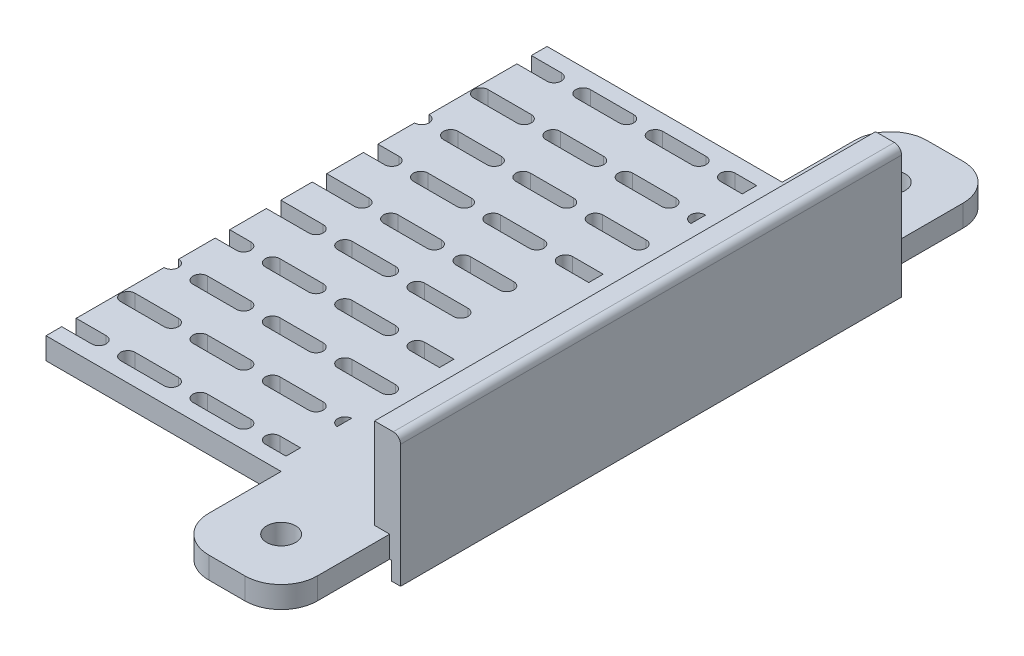
SolidWorks part; units mm, degrees
ref_plane "前视基准面" through (0, 0, 0) normal (0, 0, 1) x (1, 0, 0)
ref_plane "上视基准面" through (0, 0, 0) normal (0, 1, 0) x (1, 0, 0)
ref_plane "右视基准面" through (0, 0, 0) normal (1, 0, 0) x (0, 0, -1)
sketch "草图1" plane through (0, 0, 0) normal (0, 1, 0) x (1, 0, 0)
  line L0 (95.5, 69.25) -> (95.5, -69.25)
  line L1 (90.5, 64.25) -> (-90.5, 64.25)
  line L2 (90.5, 64.25) -> (90.5, -64.25)
  line L3 (90.5, -64.25) -> (-90.5, -64.25)
  line L4 (-90.5, 64.25) -> (-90.5, -64.25)
  line L5 (90.5, 64.25) -> (-90.5, -64.25) construction
  line L6 (90.5, -64.25) -> (-90.5, 64.25) construction
  line L7 (95.5, -69.25) -> (-95.5, -69.25)
  line L8 (-95.5, 69.25) -> (-95.5, -69.25)
  line L9 (95.5, 69.25) -> (-95.5, 69.25)
  point P0 (0, 0)
  dimension "D1" = 5
extrude "凸台-拉伸1" add sketch "草图1" along normal blind 20
sketch "草图2" plane through (0, 0, 0) normal (0, -1, 0) x (1, 0, 0)
  line L4 (-95.5, -69.25) -> (95.5, -69.25)
  line L5 (95.5, -69.25) -> (95.5, 69.25)
  line L6 (95.5, 69.25) -> (-95.5, 69.25)
  line L7 (-95.5, 69.25) -> (-95.5, -69.25)
  line L8 (-95.5, -69.25) -> (95.5, -69.25)
  line L9 (95.5, -69.25) -> (95.5, 69.25)
  line L10 (95.5, 69.25) -> (-95.5, 69.25)
  line L11 (-95.5, 69.25) -> (-95.5, -69.25)
  dimension "D1" = 0
extrude "凸台-拉伸2" add sketch "草图2" along normal blind 5
sketch "草图3" plane through (0, 0, -64.25) normal (0, 0, 1) x (1, 0, 0)
  line L4 (-90.5, 0) -> (90.5, 0)
  line L5 (90.5, 0) -> (90.5, 20)
  line L6 (90.5, 20) -> (-90.5, 20)
  line L7 (-90.5, 20) -> (-90.5, 0)
  line L8 (-90.5, 0) -> (90.5, 0)
  line L9 (90.5, 0) -> (90.5, 20)
  line L10 (90.5, 20) -> (-90.5, 20)
  line L11 (-90.5, 20) -> (-90.5, 0)
  dimension "D1" = 0
extrude "切除-拉伸1" cut sketch "草图3" against normal blind 49 and the other way blind 153
sketch "草图4" plane through (0, -5, 0) normal (0, -1, 0) x (1, 0, 0)
  line L0 (-95.5, 0) -> (-47.5, 0) construction
  line L1 (-47.5, 103) -> (47.5, 103) construction
  line L2 (-47.5, 103) -> (-47.5, -103) construction
  line L3 (-47.5, -103) -> (47.5, -103) construction
  line L4 (47.5, 103) -> (47.5, -103) construction
  line L5 (-47.5, 103) -> (47.5, -103) construction
  line L6 (-47.5, -103) -> (47.5, 103) construction
  line L7 (-95.5, 69.25) -> (-95.5, -69.25) construction
  line L8 (-95.5, 0) -> (-95.5, -35)
  line L9 (-95.5, -35) -> (-90.5, -35)
  line L10 (-90.5, -35) -> (-90.5, 35)
  line L11 (-90.5, 35) -> (-95.5, 35)
  line L12 (-95.5, 35) -> (-95.5, 0)
  line L13 (0, 0) -> (0, 35) construction
  line L14 (95.5, 35) -> (95.5, 0)
  line L15 (90.5, 35) -> (95.5, 35)
  line L16 (90.5, -35) -> (90.5, 35)
  line L17 (95.5, -35) -> (90.5, -35)
  line L18 (95.5, 0) -> (95.5, -35)
  point P0 (0, 0)
extrude "凸台-拉伸3" add sketch "草图4" along normal blind 49
sketch "草图5" plane through (0, -54, 0) normal (0, -1, 0) x (1, 0, 0)
  line L4 (-95.5, 35) -> (-95.5, -35)
  line L5 (-95.5, -35) -> (-90.5, -35)
  line L6 (-90.5, -35) -> (-90.5, 35)
  line L7 (-90.5, 35) -> (-95.5, 35)
  line L8 (-95.5, 35) -> (-95.5, -35)
  line L9 (-95.5, -35) -> (-90.5, -35)
  line L10 (-90.5, -35) -> (-90.5, 35)
  line L11 (-90.5, 35) -> (-95.5, 35)
  line L12 (95.5, 35) -> (90.5, 35)
  line L13 (90.5, 35) -> (90.5, -35)
  line L14 (90.5, -35) -> (95.5, -35)
  line L15 (95.5, -35) -> (95.5, 35)
  line L16 (95.5, 35) -> (90.5, 35)
  line L17 (90.5, 35) -> (90.5, -35)
  line L18 (90.5, -35) -> (95.5, -35)
  line L19 (95.5, -35) -> (95.5, 35)
  dimension "D1" = 0
  dimension "D2" = 0
extrude "凸台-拉伸4" add sketch "草图5" along normal blind 34
sketch "草图7" plane through (-95.5, 0, 0) normal (-1, 0, 0) x (0, 0, 1)
  line L0 (35, -88) -> (-35, -88)
  line L1 (-35, -88) -> (-35, -83)
  line L2 (-35, -88) -> (-35, -5) construction
  line L3 (-35, -83) -> (35, -83)
  line L4 (35, -88) -> (35, -5) construction
  line L5 (35, -83) -> (35, -88)
extrude "凸台-拉伸5" add sketch "草图7" along normal blind 37
sketch "草图8" plane through (95.5, 0, 0) normal (1, 0, 0) x (0, 0, -1)
  line L4 (-35, -83) -> (-35, -88)
  line L5 (35, -83) -> (-35, -83)
  line L6 (35, -88) -> (35, -83)
  line L7 (-35, -88) -> (35, -88)
  line L8 (-35, -83) -> (-35, -88)
  line L9 (35, -83) -> (-35, -83)
  line L10 (35, -88) -> (35, -83)
  line L11 (-35, -88) -> (35, -88)
  dimension "D1" = 0
extrude "凸台-拉伸6" add sketch "草图8" along normal blind 37
sketch "草图12" plane through (0, -5, 0) normal (0, -1, 0) x (1, 0, 0)
  line L0 (0, 0) -> (0, -50.9491) construction
  line L1 (0, 0) -> (21.7152, 0) construction
  line L6 (90.5, 35) -> (95.5, 35)
  line L7 (90.5, 35) -> (95.5, 35)
  line L8 (95.5, -69.25) -> (95.5, -35)
  line L9 (95.5, -35) -> (90.5, -35)
  line L10 (90.5, -35) -> (90.5, 35)
  line L11 (95.5, 35) -> (95.5, 69.25)
  line L15 (95.5, -35) -> (90.5, -35) construction
  line L16 (90.5, -35) -> (90.5, 35) construction
  line L20 (95.5, -69.25) -> (95.5, -35)
  line L27 (95.5, 35) -> (95.5, 69.25)
  line L28 (95.5, 69.25) -> (-95.5, 69.25)
  line L29 (95.5, 69.25) -> (-95.5, 69.25)
  line L30 (-95.5, 69.25) -> (-95.5, 35)
  line L31 (-95.5, 69.25) -> (-95.5, 35)
  line L32 (-95.5, 35) -> (-90.5, 35)
  line L33 (-95.5, 35) -> (-90.5, 35)
  line L34 (-90.5, 35) -> (-90.5, -35)
  line L35 (-90.5, 35) -> (-90.5, -35)
  line L36 (-90.5, -35) -> (-95.5, -35)
  line L37 (-90.5, -35) -> (-95.5, -35)
  line L38 (-95.5, -35) -> (-95.5, -69.25)
  line L39 (-95.5, -35) -> (-95.5, -69.25)
  line L40 (-95.5, -69.25) -> (95.5, -69.25)
  line L41 (-95.5, -69.25) -> (95.5, -69.25)
  circle A0 centre (48, -35) radius 12.5
  circle A1 centre (-48, -35) radius 12.5
  circle A2 centre (48, 35) radius 12.5
  circle A3 centre (-48, 35) radius 12.5
  dimension "D1" = 0
sketch "草图16" plane through (0, -88, 0) normal (0, -1, 0) x (1, 0, 0)
  line L0 (132.5, 35) -> (117.5, 35)
  line L1 (132.5, 35) -> (90.5, 35) construction
  line L2 (117.5, 35) -> (117.5, -35)
  line L3 (90.5, -35) -> (132.5, -35) construction
  line L4 (117.5, -35) -> (132.5, -35)
  line L5 (132.5, -35) -> (132.5, 35)
  line L6 (-132.5, -35) -> (-117.5, -35)
  line L7 (-132.5, -35) -> (-90.5, -35) construction
  line L8 (-117.5, -35) -> (-117.5, 35)
  line L9 (-90.5, 35) -> (-132.5, 35) construction
  line L10 (-117.5, 35) -> (-132.5, 35)
  line L11 (-132.5, 35) -> (-132.5, -35)
extrude "切除-拉伸7" cut sketch "草图16" against normal blind 62
extrude "切除-拉伸9" cut sketch "草图12" against normal blind 20 contours A0 | A1 | A3 | A2
sketch "草图19" plane through (117.5, 0, 0) normal (1, 0, 0) x (0, 0, -1)
  line L4 (-35, -83) -> (-35, -88)
  line L5 (-35, -88) -> (35, -88)
  line L6 (35, -88) -> (35, -83)
  line L7 (35, -83) -> (-35, -83)
  line L8 (-35, -83) -> (-35, -88)
  line L9 (-35, -88) -> (35, -88)
  line L10 (35, -88) -> (35, -83)
  line L11 (35, -83) -> (-35, -83)
  dimension "D1" = 0
extrude "切除-拉伸10" cut sketch "草图19" against normal blind 3.5
sketch "草图20" plane through (-117.5, 0, 0) normal (-1, 0, 0) x (0, 0, 1)
  line L4 (-35, -83) -> (-35, -88)
  line L5 (-35, -88) -> (35, -88)
  line L6 (35, -88) -> (35, -83)
  line L7 (35, -83) -> (-35, -83)
  line L8 (-35, -83) -> (-35, -88)
  line L9 (-35, -88) -> (35, -88)
  line L10 (35, -88) -> (35, -83)
  line L11 (35, -83) -> (-35, -83)
  dimension "D1" = 0
extrude "切除-拉伸11" cut sketch "草图20" against normal blind 3.5
sketch "草图21" plane through (0, -83, 0) normal (0, 1, 0) x (1, 0, 0)
  line L0 (-114, 0) -> (-95.5, 0) construction
  line L1 (-114, -35) -> (-114, 35) construction
  line L2 (-95.5, -35) -> (-95.5, 35) construction
  line L3 (-104.75, 0) -> (-104.75, -35) construction
  line L4 (-114, -35) -> (-95.5, -35) construction
  line L5 (0, 0) -> (0, 27.7926) construction
  circle A0 centre (-104.75, -17.5) radius 4
  circle A1 centre (-104.75, 17.5) radius 4
  circle A2 centre (104.75, -17.5) radius 4
  circle A3 centre (104.75, 17.5) radius 4
extrude "切除-拉伸12" cut sketch "草图21" against normal through all
fillet "圆角5" radius 10 4 edges at (114, -85.5, -35) (114, -85.5, 35) (-114, -85.5, 35) (-114, -85.5, -35)
sketch "草图22" plane through (90.5, 0, 0) normal (-1, 0, 0) x (0, 0, 1)
  line L6 (35, -88) -> (35, -5)
  line L7 (35, -5) -> (-35, -5)
  line L10 (-35, -5) -> (-35, -88)
  line L11 (-35, -88) -> (35, -88)
  line L12 (35, -88) -> (35, -5)
  line L13 (35, -5) -> (-35, -5)
  line L16 (-35, -5) -> (-35, -88)
  line L17 (-35, -88) -> (35, -88)
  dimension "D1" = 0
extrude "切除-拉伸13" cut sketch "草图22" against normal blind 54
sketch "草图23" plane through (-90.5, 0, 0) normal (1, 0, 0) x (0, 0, -1)
  line L6 (35, -5) -> (-35, -5)
  line L7 (-35, -5) -> (-35, -88)
  line L8 (-35, -88) -> (35, -88)
  line L9 (35, -88) -> (35, -5)
  line L12 (35, -5) -> (-35, -5)
  line L13 (-35, -5) -> (-35, -88)
  line L14 (-35, -88) -> (35, -88)
  line L15 (35, -88) -> (35, -5)
  dimension "D1" = 0
extrude "切除-拉伸14" cut sketch "草图23" against normal blind 54
sketch "草图24" plane through (0, -5, 0) normal (0, -1, 0) x (1, 0, 0)
  circle A1 centre (80.5, 18.25) radius 2
  circle A3 centre (80.5, -19.75) radius 2
extrude "切除-拉伸15" cut sketch "草图24" against normal blind 10
sketch "草图25" plane through (0, 0, 0) normal (0, 1, 0) x (1, 0, 0)
  circle A0 centre (80.5, -18.25) radius 4
  circle A1 centre (80.5, 19.75) radius 4
sketch "草图26" plane through (0, 0, 0) normal (0, 1, 0) x (1, 0, 0)
  line L4 (90.5, -69.25) -> (90.5, 69.25)
  line L5 (90.5, 69.25) -> (-90.5, 69.25)
  line L6 (-90.5, 69.25) -> (-90.5, -69.25)
  line L7 (-90.5, -69.25) -> (90.5, -69.25)
  line L8 (90.5, -69.25) -> (90.5, 69.25)
  line L9 (90.5, 69.25) -> (-90.5, 69.25)
  line L10 (-90.5, 69.25) -> (-90.5, -69.25)
  line L11 (-90.5, -69.25) -> (90.5, -69.25)
  circle A0 centre (48, -35) radius 12.5 construction
  circle A1 centre (48, -35) radius 12.5
  circle A2 centre (48, 35) radius 12.5 construction
  circle A3 centre (48, 35) radius 12.5
  circle A4 centre (-48, -35) radius 12.5 construction
  circle A5 centre (-48, -35) radius 12.5
  circle A6 centre (-48, 35) radius 12.5 construction
  circle A7 centre (-48, 35) radius 12.5
  dimension "D1" = 0
extrude "凸台-拉伸8" add sketch "草图26" along normal blind 1
extrude "切除-拉伸16" cut sketch "草图25" along normal blind 1 and the other way blind 4
mirror "镜向1" about plane through (0, 0, 0) normal (1, 0, 0) of "切除-拉伸15", "切除-拉伸16"
sketch "草图28" plane through (0, 1, 0) normal (0, 1, 0) x (1, 0, 0)
  circle A0 centre (-80.5, -18.25) radius 4 construction
  circle A1 centre (-80.5, -18.25) radius 4
  circle A2 centre (-80.5, 19.75) radius 4 construction
  circle A3 centre (-80.5, 19.75) radius 4
  circle A4 centre (80.5, -18.25) radius 4 construction
  circle A5 centre (80.5, -18.25) radius 4
  circle A6 centre (80.5, 19.75) radius 4 construction
  circle A7 centre (80.5, 19.75) radius 4
extrude "凸台-拉伸9" add sketch "草图28" against normal up to surface (6 mm away) up to face at (-80.5, -5, 16.25)
sketch "草图29" plane through (0, -5, 0) normal (0, -1, 0) x (1, 0, 0)
  line L0 (95.5, 69.25) -> (95, 69.25)
  line L1 (-95, 0) -> (-95, 69.25)
  line L2 (95.5, 69.25) -> (-95.5, 69.25) construction
  line L3 (-95, 69.25) -> (-95.5, 69.25)
  line L4 (-95.5, 69.25) -> (-95.5, -69.25)
  line L5 (-95.5, -69.25) -> (-95, -69.25)
  line L6 (-95.5, -69.25) -> (95.5, -69.25) construction
  line L7 (-95, -69.25) -> (-95, 0)
  line L8 (95, 69.25) -> (95, -69.25)
  line L9 (95, -69.25) -> (95.5, -69.25)
  line L10 (95.5, -69.25) -> (95.5, 69.25)
extrude "切除-拉伸18" cut sketch "草图29" against normal blind 50
sketch "草图31" plane through (0, -5, 0) normal (0, -1, 0) x (1, 0, 0)
  line L0 (-95, 69.25) -> (-95, 89.25)
  line L1 (-85, 99.25) -> (-75, 99.25)
  line L2 (-65, 89.25) -> (-65, 69.25)
  line L3 (95, 69.25) -> (-95, 69.25) construction
  line L4 (-65, 69.25) -> (-95, 69.25)
  line L5 (-80, 99.25) -> (-80, 69.25) construction
  line L6 (-80, 84.25) -> (-65, 84.25) construction
  line L7 (0, 0) -> (19.0311, 0) construction
  line L8 (0, 0) -> (0, -16.3488) construction
  line L9 (-65, -89.25) -> (-65, -69.25)
  line L10 (-85, -99.25) -> (-75, -99.25)
  line L11 (-95, -69.25) -> (-95, -89.25)
  line L12 (-65, -69.25) -> (-95, -69.25)
  line L13 (80, 84.25) -> (65, 84.25) construction
  line L14 (80, 99.25) -> (80, 69.25) construction
  line L15 (65, -69.25) -> (95, -69.25)
  line L16 (95, -69.25) -> (95, -89.25)
  line L17 (85, -99.25) -> (75, -99.25)
  line L18 (65, -89.25) -> (65, -69.25)
  line L19 (65, 69.25) -> (95, 69.25)
  line L20 (65, 89.25) -> (65, 69.25)
  line L21 (85, 99.25) -> (75, 99.25)
  line L22 (95, 69.25) -> (95, 89.25)
  arc A0 (-65, 89.25) -> (-75, 99.25) centre (-75, 89.25) ccw
  arc A1 (-95, 89.25) -> (-85, 99.25) centre (-85, 89.25) cw
  circle A2 centre (-80, 84.25) radius 4
  circle A3 centre (-80, -84.25) radius 4
  arc A4 (-65, -89.25) -> (-75, -99.25) centre (-75, -89.25) cw
  arc A5 (-95, -89.25) -> (-85, -99.25) centre (-85, -89.25) ccw
  arc A6 (95, -89.25) -> (85, -99.25) centre (85, -89.25) cw
  arc A7 (65, -89.25) -> (75, -99.25) centre (75, -89.25) ccw
  circle A8 centre (80, -84.25) radius 4
  circle A9 centre (80, 84.25) radius 4
  arc A10 (95, 89.25) -> (85, 99.25) centre (85, 89.25) ccw
  arc A11 (65, 89.25) -> (75, 99.25) centre (75, 89.25) cw
  dimension "D1" = 10
extrude "凸台-拉伸10" add sketch "草图31" against normal up to surface (6 mm away) up to face at (-48, 1, 47.5)
sketch "草图32" plane through (0, 20, 0) normal (0, 1, 0) x (1, 0, 0)
  line L0 (90.5, 69.25) -> (91.3, 69.25)
  line L4 (95, 69.25) -> (90.5, 69.25) construction
  line L5 (90.5, -69.25) -> (90.5, 69.25) construction
  line L6 (90.5, -69.25) -> (90.5, 69.25)
  line L7 (91.3, 69.25) -> (91.3, -69.25)
  line L8 (90.5, -69.25) -> (95, -69.25) construction
  line L9 (91.3, -69.25) -> (90.5, -69.25)
  line L10 (-90.5, -69.25) -> (-91.3, -69.25)
  line L11 (-95, -69.25) -> (-90.5, -69.25) construction
  line L12 (-91.3, -69.25) -> (-91.3, 69.25)
  line L13 (-90.5, 69.25) -> (-95, 69.25) construction
  line L14 (-91.3, 69.25) -> (-90.5, 69.25)
  line L15 (-90.5, 69.25) -> (-90.5, -69.25) construction
  line L16 (-90.5, 69.25) -> (-90.5, -69.25)
extrude "切除-拉伸19" cut sketch "草图32" against normal up to surface (19 mm away) up to face at (-48, 1, 47.5)
sketch "草图33" plane through (0, 20, 0) normal (0, 1, 0) x (1, 0, 0)
  line L4 (91.3, 69.25) -> (91.3, -69.25)
  line L5 (91.3, -69.25) -> (95, -69.25)
  line L6 (95, -69.25) -> (95, 69.25)
  line L7 (95, 69.25) -> (91.3, 69.25)
  line L8 (91.3, 69.25) -> (91.3, -69.25)
  line L9 (91.3, -69.25) -> (95, -69.25)
  line L10 (95, -69.25) -> (95, 69.25)
  line L11 (95, 69.25) -> (91.3, 69.25)
  line L12 (-91.3, -69.25) -> (-91.3, 69.25)
  line L13 (-91.3, 69.25) -> (-95, 69.25)
  line L14 (-95, 69.25) -> (-95, -69.25)
  line L15 (-95, -69.25) -> (-91.3, -69.25)
  line L16 (-91.3, -69.25) -> (-91.3, 69.25)
  line L17 (-91.3, 69.25) -> (-95, 69.25)
  line L18 (-95, 69.25) -> (-95, -69.25)
  line L19 (-95, -69.25) -> (-91.3, -69.25)
  dimension "D1" = 0
  dimension "D2" = 0
extrude "凸台-拉伸11" add sketch "草图33" along normal blind 6
sketch "草图34" plane through (0, -5, 0) normal (0, -1, 0) x (1, 0, 0)
  circle A0 centre (-48, -35) radius 12.5 construction
  circle A1 centre (-48, -35) radius 12.5
  circle A2 centre (-48, 35) radius 12.5 construction
  circle A3 centre (-48, 35) radius 12.5
  circle A4 centre (48, -35) radius 12.5 construction
  circle A5 centre (48, -35) radius 12.5
  circle A6 centre (48, 35) radius 12.5 construction
  circle A7 centre (48, 35) radius 12.5
extrude "凸台-拉伸12" add sketch "草图34" against normal up to surface (6 mm away) up to face at (0, 1, 0)
sketch "草图35" plane through (0, -5, 0) normal (0, -1, 0) x (1, 0, 0)
  line L0 (65, -69.25) -> (62, -69.25)
  line L2 (65, 69.25) -> (65, -69.25)
  line L6 (-65, -69.25) -> (65, -69.25) construction
  line L8 (62, -69.25) -> (62, 69.25)
  line L9 (65, 69.25) -> (-65, 69.25) construction
  line L10 (62, 69.25) -> (65, 69.25)
  line L11 (-65, -69.25) -> (-62, -69.25)
  line L12 (-62, -69.25) -> (-62, 69.25)
  line L13 (-62, 69.25) -> (-65, 69.25)
  line L14 (-65, 69.25) -> (-65, 89.25) construction
  line L15 (-65, 69.25) -> (-65, -69.25)
  point P0 (0, 0)
extrude "凸台-拉伸13" add sketch "草图35" along normal blind 5
sketch "草图36" plane through (-95, 0, 0) normal (-1, 0, 0) x (0, 0, 1)
  line L0 (-69.25, -10) -> (-69.25, -5) construction
  line L1 (-69.25, -10) -> (-69.25, -5)
  line L2 (69.25, -10) -> (69.25, -5) construction
  line L3 (69.25, -10) -> (69.25, -5)
  line L7 (-69.25, 26) -> (69.25, 26) construction
  line L8 (-69.25, 26) -> (69.25, 26)
  line L9 (69.25, 26) -> (69.25, 1) construction
  line L10 (69.25, 26) -> (69.25, 1)
  line L13 (-69.25, -10) -> (69.25, -10)
  line L16 (-69.25, 26) -> (-69.25, 1) construction
  line L17 (-69.25, 26) -> (-69.25, 1)
  line L18 (-69.25, 1) -> (-69.25, -5)
  line L19 (69.25, -5) -> (69.25, 1)
extrude "凸台-拉伸14" add sketch "草图36" along normal blind 3
sketch "草图37" plane through (-95, 0, 0) normal (1, 0, 0) x (0, 0, -1)
  line L4 (69.25, -5) -> (-69.25, -5)
  line L5 (-69.25, -5) -> (-69.25, -10)
  line L6 (-69.25, -10) -> (69.25, -10)
  line L7 (69.25, -10) -> (69.25, -5)
  line L8 (69.25, -5) -> (-69.25, -5)
  line L9 (-69.25, -5) -> (-69.25, -10)
  line L10 (-69.25, -10) -> (69.25, -10)
  line L11 (69.25, -10) -> (69.25, -5)
  dimension "D1" = 0
extrude "切除-拉伸20" cut sketch "草图37" against normal blind 0.5
mirror "镜向2" about plane through (0, 0, 0) normal (1, 0, 0) of "切除-拉伸20", "凸台-拉伸14"
sketch "草图38" plane through (0, -5, 0) normal (0, -1, 0) x (1, 0, 0)
  line L2 (0, 0) -> (62, 0)
  line L3 (62, 69.25) -> (62, -69.25) construction
  line L4 (0, -2.5) -> (-62, -2.5)
  line L5 (0, -2.5) -> (62, -2.5)
  line L6 (0, 2.5) -> (-62, 2.5)
  line L7 (0, 2.5) -> (62, 2.5)
  line L8 (-62, -69.25) -> (-62, 69.25) construction
  line L9 (-62, -2.5) -> (-62, 2.5)
  line L10 (62, 69.25) -> (62, -69.25) construction
  line L11 (62, 2.5) -> (62, -2.5)
  line L12 (0, 0) -> (-62, 0) construction
  dimension "D1" = 2.5
  dimension "D2" = 2.5
extrude "凸台-拉伸15" add sketch "草图38" along normal up to surface (5 mm away) contours L6 L9 L4 L5 L11 L7 up to face at (-63.5, -10, 0)
sketch "草图40" plane through (0, -5, 0) normal (0, -1, 0) x (1, 0, 0)
  line L0 (0, 0) -> (0, 69.25) construction
  line L1 (62, 69.25) -> (-62, 69.25) construction
  line L2 (0, 34.625) -> (-12, 34.625) construction
  line L3 (0, 34.625) -> (-32.125, 2.5) construction
  line L4 (0, 32.625) -> (-12, 32.625)
  line L5 (0, 36.625) -> (-12, 36.625)
  line L6 (62, 2.5) -> (-62, 2.5) construction
  line L7 (25, 34.625) -> (13, 34.625) construction
  line L8 (25, 32.625) -> (13, 32.625)
  line L9 (25, 36.625) -> (13, 36.625)
  line L10 (50, 34.625) -> (38, 34.625) construction
  line L11 (50, 32.625) -> (38, 32.625)
  line L12 (50, 36.625) -> (38, 36.625)
  line L13 (-25, 34.625) -> (-37, 34.625) construction
  line L14 (-25, 32.625) -> (-37, 32.625)
  line L15 (-25, 36.625) -> (-37, 36.625)
  arc A0 (0, 32.625) -> (0, 36.625) centre (0, 34.625) ccw
  arc A1 (-12, 36.625) -> (-12, 32.625) centre (-12, 34.625) ccw
  arc A2 (25, 32.625) -> (25, 36.625) centre (25, 34.625) ccw
  arc A3 (13, 36.625) -> (13, 32.625) centre (13, 34.625) ccw
  arc A4 (50, 32.625) -> (50, 36.625) centre (50, 34.625) ccw
  arc A5 (38, 36.625) -> (38, 32.625) centre (38, 34.625) ccw
  arc A6 (-25, 32.625) -> (-25, 36.625) centre (-25, 34.625) ccw
  arc A7 (-37, 36.625) -> (-37, 32.625) centre (-37, 34.625) ccw
  point P9 (-6, 34.625)
  point P20 (19, 34.625)
  point P27 (44, 34.625)
  point P34 (-31, 34.625)
  dimension "D1" = 45
  dimension "D2" = 3
  dimension "D3" = 2
extrude "切除-拉伸22" cut sketch "草图40" against normal through all contours L5 A1 L4 A0
sketch "草图41" plane through (0, -5, 0) normal (0, -1, 0) x (1, 0, 0)
  line L0 (0, 0) -> (0, 69.25)
  line L1 (62, 69.25) -> (-62, 69.25) construction
  line L2 (0, 34.625) -> (-32.125, 2.5)
  line L3 (62, 2.5) -> (-62, 2.5) construction
  dimension "D1" = 45
pattern_linear "阵列(线性)1" count 3 spacing 20 along (-0.7071, 0, -0.7071) of "切除-拉伸22"
pattern_linear "阵列(线性)2" count 3 spacing 20 along (0.7071, 0, 0.7071) of "切除-拉伸22"
pattern_linear "阵列(线性)3" count 5 spacing 20 along (1, 0, 0) of "阵列(线性)2", "阵列(线性)1", "切除-拉伸22"
sketch "草图42" plane through (0, 1, 0) normal (0, 1, 0) x (1, 0, 0)
  line L0 (82.1421, -50.7671) -> (91.3, -50.7671) construction
  line L1 (82.1421, -50.7671) -> (91.3, -50.7671)
  line L2 (82.1421, -46.7671) -> (91.3, -46.7671) construction
  line L3 (82.1421, -46.7671) -> (91.3, -46.7671)
  line L4 (94.1421, -46.7671) -> (91.3, -46.7671) construction
  line L5 (94.1421, -46.7671) -> (91.3, -46.7671)
  line L6 (94.1421, -50.7671) -> (91.3, -50.7671) construction
  line L7 (94.1421, -50.7671) -> (91.3, -50.7671)
  line L8 (98, -64.9093) -> (96.2843, -64.9093) construction
  line L9 (98, -64.9093) -> (96.2843, -64.9093)
  line L10 (98, -60.9093) -> (96.2843, -60.9093) construction
  line L11 (98, -60.9093) -> (96.2843, -60.9093)
  line L12 (98, -64.9093) -> (98, -60.9093) construction
  line L13 (98, -64.9093) -> (98, -60.9093)
  line L14 (76.2843, -60.9093) -> (88.2843, -60.9093) construction
  line L15 (76.2843, -60.9093) -> (88.2843, -60.9093)
  line L16 (76.2843, -64.9093) -> (88.2843, -64.9093) construction
  line L17 (76.2843, -64.9093) -> (88.2843, -64.9093)
  line L20 (56.2843, -60.9093) -> (68.2843, -60.9093) construction
  line L21 (65, -60.9093) -> (68.2843, -60.9093)
  line L22 (56.2843, -64.9093) -> (68.2843, -64.9093) construction
  line L23 (65, -64.9093) -> (68.2843, -64.9093)
  line L26 (62.1421, -50.7671) -> (74.1421, -50.7671) construction
  line L27 (62.1421, -46.7671) -> (74.1421, -46.7671) construction
  line L28 (65, -50.7671) -> (74.1421, -50.7671)
  line L29 (65, -46.7671) -> (74.1421, -46.7671)
  line L30 (68, -32.625) -> (80, -32.625) construction
  line L31 (68, -36.625) -> (80, -36.625) construction
  line L32 (68, -32.625) -> (80, -32.625)
  line L33 (68, -36.625) -> (80, -36.625)
  line L34 (53.8579, -22.4829) -> (65.8579, -22.4829) construction
  line L35 (53.8579, -18.4829) -> (65.8579, -18.4829) construction
  line L37 (65, -22.4829) -> (65.8579, -22.4829)
  line L38 (65, -18.4829) -> (65.8579, -18.4829)
  line L44 (62, -64.9093) -> (65, -64.9093)
  line L45 (65, -64.9093) -> (65, -60.9093)
  line L46 (65, -60.9093) -> (62, -60.9093)
  line L47 (62, -60.9093) -> (62, -64.9093)
  line L48 (62, -64.9093) -> (65, -64.9093)
  line L49 (62.1421, -50.7671) -> (65, -50.7671)
  line L50 (65, -60.9093) -> (62, -60.9093)
  line L51 (62, -60.9093) -> (62, -64.9093)
  line L52 (65, -50.7671) -> (65, -46.7671)
  line L53 (65, -46.7671) -> (62.1421, -46.7671)
  line L54 (62, -46.7722) -> (62, -50.7621)
  line L55 (62.1421, -50.7671) -> (65, -50.7671)
  line L56 (62, -22.4829) -> (65, -22.4829)
  line L57 (65, -46.7671) -> (62.1421, -46.7671)
  line L58 (62, -46.7722) -> (62, -50.7621)
  line L59 (65, -22.4829) -> (65, -18.4829)
  line L60 (65, -18.4829) -> (62, -18.4829)
  line L61 (62, -18.4829) -> (62, -22.4829)
  line L62 (62, -22.4829) -> (65, -22.4829)
  line L64 (65, -18.4829) -> (62, -18.4829)
  line L65 (62, -18.4829) -> (62, -22.4829)
  arc A0 (82.1421, -46.7671) -> (82.1421, -50.7671) centre (82.1421, -48.7671) ccw construction
  arc A1 (82.1421, -46.7671) -> (82.1421, -50.7671) centre (82.1421, -48.7671) ccw
  arc A2 (95.5, -50.2355) -> (95.5, -47.2987) centre (94.1421, -48.7671) ccw construction
  arc A3 (95.5, -50.2355) -> (95.5, -47.2987) centre (94.1421, -48.7671) ccw
  arc A4 (95.5, -47.2987) -> (94.1421, -46.7671) centre (94.1421, -48.7671) ccw construction
  arc A5 (95.5, -47.2987) -> (94.1421, -46.7671) centre (94.1421, -48.7671) ccw
  arc A6 (94.1421, -50.7671) -> (95.5, -50.2355) centre (94.1421, -48.7671) ccw construction
  arc A7 (94.1421, -50.7671) -> (95.5, -50.2355) centre (94.1421, -48.7671) ccw
  arc A8 (96.2843, -60.9093) -> (96.2843, -64.9093) centre (96.2843, -62.9093) ccw construction
  arc A9 (96.2843, -60.9093) -> (96.2843, -64.9093) centre (96.2843, -62.9093) ccw
  arc A10 (88.2843, -64.9093) -> (88.2843, -60.9093) centre (88.2843, -62.9093) ccw construction
  arc A11 (88.2843, -64.9093) -> (88.2843, -60.9093) centre (88.2843, -62.9093) ccw
  arc A12 (76.2843, -60.9093) -> (76.2843, -64.9093) centre (76.2843, -62.9093) ccw construction
  arc A13 (76.2843, -60.9093) -> (76.2843, -64.9093) centre (76.2843, -62.9093) ccw
  arc A14 (68.2843, -64.9093) -> (68.2843, -60.9093) centre (68.2843, -62.9093) ccw construction
  arc A15 (68.2843, -64.9093) -> (68.2843, -60.9093) centre (68.2843, -62.9093) ccw
  arc A16 (74.1421, -50.7671) -> (74.1421, -46.7671) centre (74.1421, -48.7671) ccw construction
  arc A17 (74.1421, -50.7671) -> (74.1421, -46.7671) centre (74.1421, -48.7671) ccw
  arc A18 (68, -32.625) -> (68, -36.625) centre (68, -34.625) ccw construction
  arc A19 (80, -36.625) -> (80, -32.625) centre (80, -34.625) ccw construction
  arc A20 (68, -32.625) -> (68, -36.625) centre (68, -34.625) ccw
  arc A21 (80, -36.625) -> (80, -32.625) centre (80, -34.625) ccw
  arc A22 (65.8579, -22.4829) -> (65.8579, -18.4829) centre (65.8579, -20.4829) ccw construction
  arc A23 (65.8579, -22.4829) -> (65.8579, -18.4829) centre (65.8579, -20.4829) ccw
  arc A26 (62, -50.7621) -> (62.1421, -50.7671) centre (62.1421, -48.7671) ccw
  arc A27 (62.1421, -46.7671) -> (62, -46.7722) centre (62.1421, -48.7671) ccw
  arc A28 (62, -50.7621) -> (62.1421, -50.7671) centre (62.1421, -48.7671) ccw
  arc A29 (62.1421, -46.7671) -> (62, -46.7722) centre (62.1421, -48.7671) ccw
  dimension "D1" = 0
  dimension "D2" = 0
  dimension "D3" = 0
extrude "凸台-拉伸16" add sketch "草图42" against normal up to surface (6 mm away) up to face at (63.5, -5, 62.9093)
sketch "草图43" plane through (0, 1, 0) normal (0, 1, 0) x (1, 0, 0)
  line L0 (94.1421, -46.7671) -> (91.3, -46.7671) construction
  line L1 (94.1421, -46.7671) -> (91.3, -46.7671)
  line L2 (94.1421, -50.7671) -> (91.3, -50.7671) construction
  line L3 (96.2843, -64.9093) -> (98, -64.9093)
  line L4 (98, -64.9093) -> (98, -60.9093)
  line L5 (98, -60.9093) -> (96.2843, -60.9093)
  line L6 (96.2843, -64.9093) -> (98, -64.9093)
  line L7 (98, -64.9093) -> (98, -60.9093)
  line L8 (98, -60.9093) -> (96.2843, -60.9093)
  line L9 (94.1421, -50.7671) -> (91.3, -50.7671)
  line L10 (91.3, -50.7671) -> (91.3, -46.7671)
  arc A0 (94.1421, -50.7671) -> (94.1421, -46.7671) centre (94.1421, -48.7671) ccw construction
  arc A1 (96.2843, -60.9093) -> (96.2843, -64.9093) centre (96.2843, -62.9093) ccw
  arc A2 (96.2843, -60.9093) -> (96.2843, -64.9093) centre (96.2843, -62.9093) ccw
  arc A3 (94.1421, -50.7671) -> (94.1421, -46.7671) centre (94.1421, -48.7671) ccw
  dimension "D1" = 0
extrude "凸台-拉伸17" add sketch "草图43" along normal up to surface (25 mm away)
pattern_linear "阵列(线性)4" count 5 spacing 20 along (-1, 0, 0) of "阵列(线性)1", "阵列(线性)2", "切除-拉伸22"
sketch "草图44" plane through (0, 1, 0) normal (0, 1, 0) x (1, 0, 0)
  line L0 (-63.7157, -64.9093) -> (-51.7157, -64.9093) construction
  line L1 (-63.7157, -60.9093) -> (-51.7157, -60.9093) construction
  line L2 (-62, -60.9093) -> (-62, -64.9093) construction
  line L3 (-62, -32.625) -> (-62, -36.625) construction
  line L4 (-72, -32.625) -> (-60, -32.625) construction
  line L5 (-72, -36.625) -> (-60, -36.625) construction
  line L7 (-77.8579, -50.7671) -> (-65.8579, -50.7671) construction
  line L8 (-77.8579, -46.7671) -> (-65.8579, -46.7671) construction
  line L9 (-63.7157, -64.9093) -> (-62, -64.9093)
  line L10 (-63.7157, -60.9093) -> (-62, -60.9093)
  line L11 (-62, -60.9093) -> (-62, -64.9093)
  line L12 (-62, -32.625) -> (-62, -36.625)
  line L13 (-72, -32.625) -> (-62, -32.625)
  line L14 (-72, -36.625) -> (-62, -36.625)
  line L16 (-77.8579, -50.7671) -> (-65.8579, -50.7671)
  line L17 (-77.8579, -46.7671) -> (-65.8579, -46.7671)
  line L18 (-98, -4.3407) -> (-98, -8.3407) construction
  line L19 (-62, -18.4829) -> (-62, -22.4829) construction
  line L20 (-66.1421, -22.4829) -> (-54.1421, -22.4829) construction
  line L21 (-66.1421, -18.4829) -> (-54.1421, -18.4829) construction
  line L22 (-62, -5.313) -> (-62, -7.3685) construction
  line L23 (-80.2843, -8.3407) -> (-68.2843, -8.3407) construction
  line L24 (-80.2843, -4.3407) -> (-68.2843, -4.3407) construction
  line L25 (-91.3, -8.3407) -> (-88.2843, -8.3407) construction
  line L26 (-91.3, -4.3407) -> (-88.2843, -4.3407) construction
  line L27 (-91.3, -4.3407) -> (-98, -4.3407) construction
  line L28 (-91.3, -8.3407) -> (-98, -8.3407) construction
  line L29 (-98, -4.3407) -> (-98, -8.3407)
  line L30 (-91.3, -8.3407) -> (-98, -8.3407)
  line L31 (-91.3, -4.3407) -> (-98, -4.3407)
  line L32 (-91.3, -4.3407) -> (-88.2843, -4.3407)
  line L33 (-91.3, -8.3407) -> (-88.2843, -8.3407)
  line L34 (-80.2843, -4.3407) -> (-68.2843, -4.3407)
  line L35 (-80.2843, -8.3407) -> (-68.2843, -8.3407)
  line L36 (-62, -5.313) -> (-62, -7.3685)
  line L37 (-66.1421, -18.4829) -> (-62, -18.4829)
  line L38 (-66.1421, -22.4829) -> (-62, -22.4829)
  line L39 (-62, -18.4829) -> (-62, -22.4829)
  line L40 (-91.3, -36.625) -> (-80, -36.625) construction
  line L41 (-92, -36.625) -> (-91.3, -36.625) construction
  line L42 (-92, -32.625) -> (-91.3, -32.625) construction
  line L43 (-91.3, -32.625) -> (-80, -32.625) construction
  line L44 (-86.1421, -22.4829) -> (-74.1421, -22.4829) construction
  line L45 (-86.1421, -18.4829) -> (-74.1421, -18.4829) construction
  line L46 (-94.1421, -22.4829) -> (-98, -22.4829) construction
  line L47 (-94.1421, -18.4829) -> (-98, -18.4829) construction
  line L48 (-98, -18.4829) -> (-98, -22.4829) construction
  line L49 (-91.3, -36.625) -> (-80, -36.625)
  line L50 (-92, -36.625) -> (-91.3, -36.625)
  line L51 (-92, -32.625) -> (-91.3, -32.625)
  line L52 (-91.3, -32.625) -> (-80, -32.625)
  line L53 (-86.1421, -22.4829) -> (-74.1421, -22.4829)
  line L54 (-86.1421, -18.4829) -> (-74.1421, -18.4829)
  line L55 (-94.1421, -22.4829) -> (-98, -22.4829)
  line L56 (-94.1421, -18.4829) -> (-98, -18.4829)
  line L57 (-98, -18.4829) -> (-98, -22.4829)
  arc A0 (-63.7157, -60.9093) -> (-63.7157, -64.9093) centre (-63.7157, -62.9093) ccw construction
  arc A1 (-72, -32.625) -> (-72, -36.625) centre (-72, -34.625) ccw construction
  arc A2 (-65.8579, -50.7671) -> (-65.8579, -46.7671) centre (-65.8579, -48.7671) ccw construction
  arc A3 (-77.8579, -46.7671) -> (-77.8579, -50.7671) centre (-77.8579, -48.7671) ccw construction
  arc A4 (-63.7157, -60.9093) -> (-63.7157, -64.9093) centre (-63.7157, -62.9093) ccw
  arc A5 (-72, -32.625) -> (-72, -36.625) centre (-72, -34.625) ccw
  arc A7 (-77.8579, -46.7671) -> (-77.8579, -50.7671) centre (-77.8579, -48.7671) ccw
  arc A8 (-66.1421, -18.4829) -> (-66.1421, -22.4829) centre (-66.1421, -20.4829) ccw construction
  arc A9 (-60.2843, -4.3407) -> (-60.2843, -8.3407) centre (-60.2843, -6.3407) ccw construction
  arc A10 (-68.2843, -8.3407) -> (-68.2843, -4.3407) centre (-68.2843, -6.3407) ccw construction
  arc A11 (-80.2843, -4.3407) -> (-80.2843, -8.3407) centre (-80.2843, -6.3407) ccw construction
  arc A12 (-88.2843, -8.3407) -> (-88.2843, -4.3407) centre (-88.2843, -6.3407) ccw construction
  arc A13 (-88.2843, -8.3407) -> (-88.2843, -4.3407) centre (-88.2843, -6.3407) ccw
  arc A14 (-80.2843, -4.3407) -> (-80.2843, -8.3407) centre (-80.2843, -6.3407) ccw
  arc A15 (-68.2843, -8.3407) -> (-68.2843, -4.3407) centre (-68.2843, -6.3407) ccw
  arc A16 (-62, -5.313) -> (-62, -7.3685) centre (-60.2843, -6.3407) ccw
  arc A17 (-66.1421, -18.4829) -> (-66.1421, -22.4829) centre (-66.1421, -20.4829) ccw
  arc A18 (-80, -36.625) -> (-80, -32.625) centre (-80, -34.625) ccw construction
  arc A19 (-92, -32.625) -> (-92, -36.625) centre (-92, -34.625) ccw construction
  arc A20 (-74.1421, -22.4829) -> (-74.1421, -18.4829) centre (-74.1421, -20.4829) ccw construction
  arc A21 (-86.1421, -18.4829) -> (-86.1421, -22.4829) centre (-86.1421, -20.4829) ccw construction
  arc A22 (-94.1421, -22.4829) -> (-94.1421, -18.4829) centre (-94.1421, -20.4829) ccw construction
  arc A23 (-80, -36.625) -> (-80, -32.625) centre (-80, -34.625) ccw
  arc A24 (-92, -32.625) -> (-92, -36.625) centre (-92, -34.625) ccw
  arc A25 (-74.1421, -22.4829) -> (-74.1421, -18.4829) centre (-74.1421, -20.4829) ccw
  arc A26 (-86.1421, -18.4829) -> (-86.1421, -22.4829) centre (-86.1421, -20.4829) ccw
  arc A27 (-94.1421, -22.4829) -> (-94.1421, -18.4829) centre (-94.1421, -20.4829) ccw
  arc A29 (-65.8579, -50.7671) -> (-65.8579, -46.7671) centre (-65.8579, -48.7671) ccw
extrude "凸台-拉伸18" add sketch "草图44" against normal up to surface (6 mm away)
sketch "草图45" plane through (0, 1, 0) normal (0, 1, 0) x (1, 0, 0)
  line L0 (-91.3, -4.3407) -> (-98, -4.3407) construction
  line L1 (-91.3, -4.3407) -> (-98, -4.3407)
  line L2 (-91.3, -8.3407) -> (-98, -8.3407) construction
  line L3 (-91.3, -8.3407) -> (-98, -8.3407)
  line L4 (-98, -4.3407) -> (-98, -8.3407) construction
  line L5 (-98, -4.3407) -> (-98, -8.3407)
  line L6 (-92, -32.625) -> (-91.3, -32.625) construction
  line L7 (-92, -32.625) -> (-91.3, -32.625)
  line L8 (-92, -36.625) -> (-91.3, -36.625) construction
  line L9 (-94.1421, -18.4829) -> (-98, -18.4829)
  line L10 (-98, -18.4829) -> (-98, -22.4829)
  line L11 (-98, -22.4829) -> (-94.1421, -22.4829)
  line L12 (-94.1421, -18.4829) -> (-98, -18.4829)
  line L13 (-98, -18.4829) -> (-98, -22.4829)
  line L14 (-98, -22.4829) -> (-94.1421, -22.4829)
  line L15 (-92, -36.625) -> (-91.3, -36.625)
  line L16 (-91.3, -8.3407) -> (-91.3, -4.3407)
  line L17 (-91.3, -32.625) -> (-91.3, -36.625)
  arc A0 (-92, -32.625) -> (-92, -36.625) centre (-92, -34.625) ccw construction
  arc A1 (-94.1421, -22.4829) -> (-94.1421, -18.4829) centre (-94.1421, -20.4829) ccw
  arc A2 (-94.1421, -22.4829) -> (-94.1421, -18.4829) centre (-94.1421, -20.4829) ccw
  arc A3 (-92, -32.625) -> (-92, -36.625) centre (-92, -34.625) ccw
  dimension "D1" = 0
extrude "凸台-拉伸19" add sketch "草图45" along normal up to surface (25 mm away)
mirror "镜向5" about plane through (0, 0, 0) normal (0, 0, 1) of "阵列(线性)4", "阵列(线性)3", "阵列(线性)2", "阵列(线性)1", "切除-拉伸22"
sketch "草图46" plane through (0, 1, 0) normal (0, 1, 0) x (1, 0, 0)
  line L10 (62.2843, 60.9093) -> (62.2843, 69.25)
  line L11 (56.2843, 60.9093) -> (68.2843, 60.9093) construction
  line L12 (65, 69.25) -> (-65, 69.25) construction
  line L13 (98, 64.9093) -> (98, 69.25) construction
  line L14 (98, 64.9093) -> (98, 69.25)
  line L15 (62.2843, 69.25) -> (98, 69.25)
  line L16 (62.2843, 60.9093) -> (62.2843, 4.433)
  line L17 (62.2843, 4.433) -> (98, 4.433)
  line L18 (98, 4.433) -> (98, 64.9093)
  line L19 (0, 0) -> (0, 15.6294) construction
  line L20 (-62.2843, 4.433) -> (-98, 4.433)
  line L21 (-62.2843, 60.9093) -> (-62.2843, 4.433)
  line L22 (-62.2843, 60.9093) -> (-62.2843, 69.25)
  line L23 (-62.2843, 69.25) -> (-98, 69.25)
  line L24 (-98, 64.9093) -> (-98, 69.25)
  line L25 (-98, 4.433) -> (-98, 64.9093)
extrude "凸台-拉伸20" add sketch "草图46" against normal up to surface (6 mm away) up to face at (-34.2843, -5, -6.3407)
sketch "草图47" plane through (0, 1, 0) normal (0, 1, 0) x (1, 0, 0)
  line L0 (-98, 4.433) -> (-98, 4.3407) construction
  line L1 (-62, 5.313) -> (-62, 7.3685)
  line L2 (-62, 5.313) -> (-62, 7.3685)
  line L3 (-98, 4.433) -> (-98, 4.3407)
  line L4 (-62, 22.4829) -> (-62.2843, 22.4829)
  line L5 (-62.2843, 22.4829) -> (-62.2843, 18.4829)
  line L6 (-62.2843, 18.4829) -> (-62, 18.4829)
  line L7 (-62, 18.4829) -> (-62, 22.4829)
  line L8 (-62, 22.4829) -> (-62.2843, 22.4829)
  line L9 (-62.2843, 22.4829) -> (-62.2843, 18.4829)
  line L10 (-62.2843, 18.4829) -> (-62, 18.4829)
  line L11 (-62, 18.4829) -> (-62, 22.4829)
  line L12 (-98, 4.433) -> (-87.6837, 4.433) construction
  line L13 (-98, 4.433) -> (-87.6837, 4.433)
  line L14 (-62, 36.625) -> (-62.2843, 36.625)
  line L15 (-62.2843, 36.625) -> (-62.2843, 32.625)
  line L16 (-62.2843, 32.625) -> (-62, 32.625)
  line L17 (-62, 32.625) -> (-62, 36.625)
  line L18 (-62, 36.625) -> (-62.2843, 36.625)
  line L19 (-62.2843, 36.625) -> (-62.2843, 32.625)
  line L20 (-62.2843, 32.625) -> (-62, 32.625)
  line L21 (-62, 32.625) -> (-62, 36.625)
  line L22 (-62, 64.9093) -> (-62.2843, 64.9093)
  line L23 (-62.2843, 64.9093) -> (-62.2843, 60.9093)
  line L24 (-62.2843, 60.9093) -> (-62, 60.9093)
  line L25 (-62, 60.9093) -> (-62, 64.9093)
  line L26 (-62, 64.9093) -> (-62.2843, 64.9093)
  line L27 (-62.2843, 64.9093) -> (-62.2843, 60.9093)
  line L28 (-62.2843, 60.9093) -> (-62, 60.9093)
  line L29 (-62, 60.9093) -> (-62, 64.9093)
  line L30 (-91.3, 4.3407) -> (-88.2843, 4.3407) construction
  line L31 (-91.3, 4.3407) -> (-88.2843, 4.3407)
  line L32 (-91.3, 4.3407) -> (-98, 4.3407) construction
  line L33 (-91.3, 4.3407) -> (-98, 4.3407)
  line L34 (-80.8849, 4.433) -> (-67.6837, 4.433) construction
  line L35 (-80.8849, 4.433) -> (-67.6837, 4.433)
  line L36 (-80.2843, 4.3407) -> (-68.2843, 4.3407) construction
  line L37 (-80.2843, 4.3407) -> (-68.2843, 4.3407)
  arc A0 (-88.2843, 4.3407) -> (-87.6837, 4.433) centre (-88.2843, 6.3407) ccw construction
  arc A1 (-62, 7.3685) -> (-62, 5.313) centre (-60.2843, 6.3407) ccw
  arc A2 (-62, 7.3685) -> (-62, 5.313) centre (-60.2843, 6.3407) ccw
  arc A3 (-88.2843, 4.3407) -> (-87.6837, 4.433) centre (-88.2843, 6.3407) ccw
  arc A4 (-68.2843, 4.3407) -> (-67.6837, 4.433) centre (-68.2843, 6.3407) ccw construction
  arc A5 (-68.2843, 4.3407) -> (-67.6837, 4.433) centre (-68.2843, 6.3407) ccw
  arc A6 (-80.8849, 4.433) -> (-80.2843, 4.3407) centre (-80.2843, 6.3407) ccw construction
  arc A7 (-80.8849, 4.433) -> (-80.2843, 4.3407) centre (-80.2843, 6.3407) ccw
  dimension "D1" = 0
  dimension "D2" = 0
  dimension "D3" = 0
  dimension "D4" = 0
extrude "凸台-拉伸21" add sketch "草图47" against normal up to surface (6 mm away) up to face at (-62.1421, -5, -20.4829)
sketch "草图48" plane through (0, 1, 0) normal (0, 1, 0) x (1, 0, 0)
  line L0 (-91.3, 36.625) -> (-92, 36.625) construction
  line L1 (-91.3, 36.625) -> (-92, 36.625)
  line L2 (-92, 32.625) -> (-91.3, 32.625) construction
  line L3 (-94.1421, 22.4829) -> (-98, 22.4829)
  line L4 (-98, 22.4829) -> (-98, 18.4829)
  line L5 (-98, 18.4829) -> (-94.1421, 18.4829)
  line L6 (-94.1421, 22.4829) -> (-98, 22.4829)
  line L7 (-98, 22.4829) -> (-98, 18.4829)
  line L8 (-98, 18.4829) -> (-94.1421, 18.4829)
  line L9 (-92, 32.625) -> (-91.3, 32.625)
  line L10 (-91.3, 8.3407) -> (-98, 8.3407) construction
  line L11 (-91.3, 8.3407) -> (-98, 8.3407)
  line L12 (-98, 8.3407) -> (-98, 4.3407) construction
  line L13 (-98, 8.3407) -> (-98, 4.3407)
  line L14 (-91.3, 4.3407) -> (-98, 4.3407) construction
  line L15 (-91.3, 4.3407) -> (-98, 4.3407)
  line L16 (94.1421, 50.7671) -> (91.3, 50.7671) construction
  line L17 (94.1421, 50.7671) -> (91.3, 50.7671)
  line L18 (94.1421, 46.7671) -> (91.3, 46.7671) construction
  line L19 (98, 60.9093) -> (98, 64.9093)
  line L20 (98, 64.9093) -> (96.2843, 64.9093)
  line L21 (96.2843, 60.9093) -> (98, 60.9093)
  line L22 (98, 60.9093) -> (98, 64.9093)
  line L23 (98, 64.9093) -> (96.2843, 64.9093)
  line L24 (96.2843, 60.9093) -> (98, 60.9093)
  line L25 (94.1421, 46.7671) -> (91.3, 46.7671)
  line L26 (91.3, 46.7671) -> (91.3, 50.7671)
  line L27 (-91.3, 4.3407) -> (-91.3, 8.3407)
  line L28 (-91.3, 32.625) -> (-91.3, 36.625)
  arc A0 (-92, 36.625) -> (-92, 32.625) centre (-92, 34.625) ccw construction
  arc A1 (-94.1421, 18.4829) -> (-94.1421, 22.4829) centre (-94.1421, 20.4829) ccw
  arc A2 (-94.1421, 18.4829) -> (-94.1421, 22.4829) centre (-94.1421, 20.4829) ccw
  arc A3 (-92, 36.625) -> (-92, 32.625) centre (-92, 34.625) ccw
  arc A4 (94.1421, 46.7671) -> (94.1421, 50.7671) centre (94.1421, 48.7671) ccw construction
  arc A5 (96.2843, 64.9093) -> (96.2843, 60.9093) centre (96.2843, 62.9093) ccw
  arc A6 (96.2843, 64.9093) -> (96.2843, 60.9093) centre (96.2843, 62.9093) ccw
  arc A7 (94.1421, 46.7671) -> (94.1421, 50.7671) centre (94.1421, 48.7671) ccw
  dimension "D1" = 0
  dimension "D2" = 0
extrude "凸台-拉伸22" add sketch "草图48" along normal up to surface (25 mm away)
fillet "圆角6" radius 2 2 edges at (-98, 26, 0) (98, 26, 0)
sketch "草图49" plane through (0, 26, 0) normal (0, 1, 0) x (1, 0, 0)
  line L0 (-91.3, -69.25) -> (-90.8, -69.25)
  line L1 (-91.3, 69.25) -> (-90.8, 69.25)
  line L2 (-90.8, 69.25) -> (-90.8, -69.25)
  line L3 (-91.3, -69.25) -> (-91.3, 69.25) construction
  line L4 (-91.3, -69.25) -> (-91.3, 69.25)
  line L5 (0, 0) -> (0, 30.0446) construction
  line L6 (91.3, -69.25) -> (91.3, 69.25)
  line L7 (90.8, 69.25) -> (90.8, -69.25)
  line L8 (91.3, 69.25) -> (90.8, 69.25)
  line L9 (91.3, -69.25) -> (90.8, -69.25)
extrude "凸台-拉伸23" add sketch "草图49" against normal up to surface (25 mm away) up to face at (-56.3579, 1, -62.9093)
sketch "草图50" plane through (0, 1, 0) normal (0, 1, 0) x (1, 0, 0)
  line L0 (0, 0) -> (0, -69.25)
  line L1 (-65, -69.25) -> (65, -69.25) construction
  line L2 (0, -69.25) -> (-40.4862, -102.9961)
  line L3 (-40.4862, -102.9961) -> (-139.3941, -111.1725)
  line L4 (-139.3941, -111.1725) -> (-154.6918, -102.9961)
  line L6 (-154.6918, -102.9961) -> (-141.5041, 77.9394)
  line L7 (-141.5041, 77.9394) -> (-113.6958, 101.1183)
  line L8 (-113.6958, 101.1183) -> (-108.4559, 105.4859)
  line L9 (-108.4559, 105.4859) -> (-40.4862, 96.9297)
  line L10 (-40.4862, 96.9297) -> (0, 69.25)
  line L11 (65, 69.25) -> (-65, 69.25) construction
  line L12 (0, 69.25) -> (0, 0)
extrude "切除-拉伸23" cut sketch "草图50" against normal through all and the other way through all
